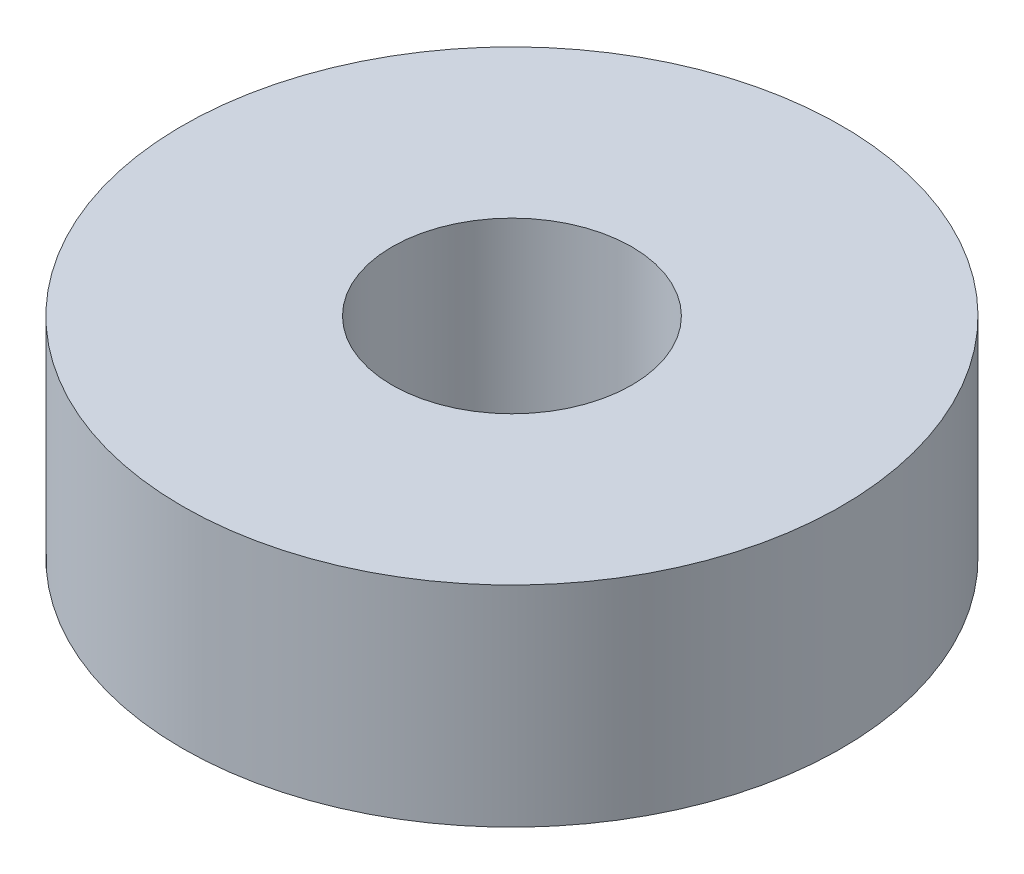
SolidWorks part; units mm, degrees
material "AISI 4340 Steel, normalized"
ref_plane "Front Plane" through (0, 0, 0) normal (0, 0, 1) x (1, 0, 0)
ref_plane "Top Plane" through (0, 0, 0) normal (0, 1, 0) x (1, 0, 0)
ref_plane "Right Plane" through (0, 0, 0) normal (1, 0, 0) x (0, 0, -1)
sketch "Sketch1" plane through (0, 0, 0) normal (0, 1, 0) x (1, 0, 0)
  circle A0 centre (0, 0) radius 11
  circle A1 centre (0, 0) radius 4
  dimension "D1" = 8
  dimension "D2" = 22
extrude "Boss-Extrude1" add sketch "Sketch1" along normal blind 7 contours A0
equation "\"pulley_pitch_diam\"= 12.73mm"
equation "\"pulley_total_width\"= 16mm"
equation "\"pulley_total_diam\"= 16mm"
equation "\"belt_width\"= 6mm"
equation "\"material_thickness\"= 3mm"
equation "\"shaft_diam\"= 8mm"
equation "\"bearing_od\"= 22mm"
equation "\"bearing_thickness\"= 7mm"
equation "\"D1@Sketch1\"=\"shaft_diam\""
equation "\"D2@Sketch1\"=\"bearing_od\""
equation "\"D1@Boss-Extrude1\"=\"bearing_thickness\""
